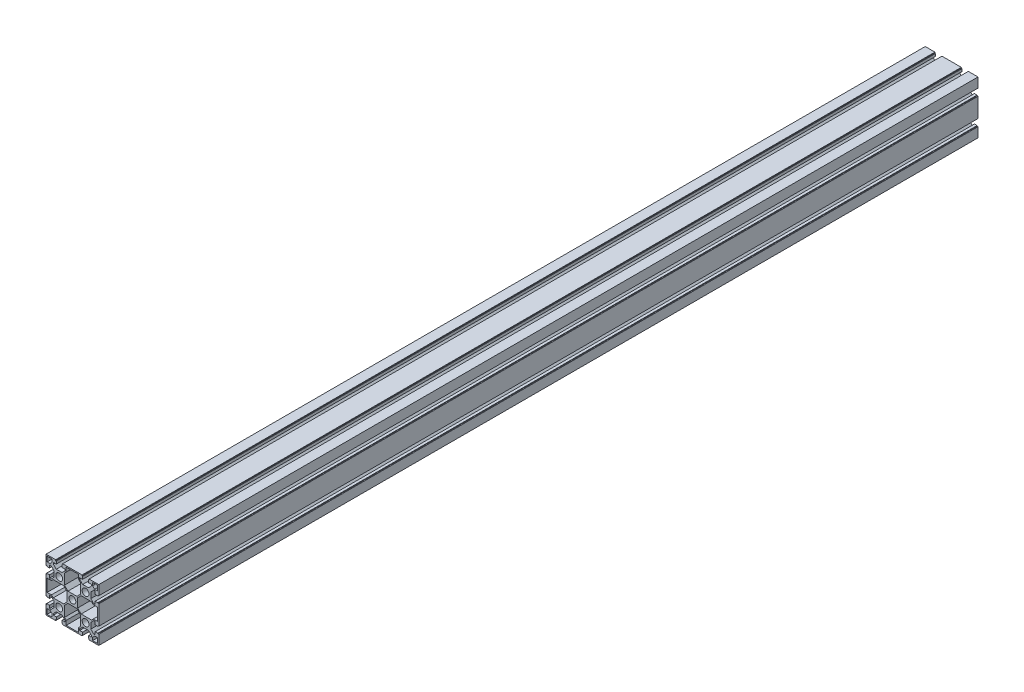
SolidWorks part; units mm, degrees
ref_plane "Alzado" through (0, 0, 0) normal (0, 0, 1) x (1, 0, 0)
ref_plane "Planta" through (0, 0, 0) normal (0, 1, 0) x (1, 0, 0)
ref_plane "Vista lateral" through (0, 0, 0) normal (1, 0, 0) x (0, 0, -1)
sketch "Croquis1" plane through (0, 0, 0) normal (0, 0, 1) x (1, 0, 0)
  line L0 (-1000, 0) -> (49000, 0) construction
  line L1 (0, -1000) -> (0, 49000) construction
  line L2 (-22.5, -999.7728) -> (-22.5, 49000.2272) construction
  line L7 (22.5, -999.7728) -> (22.5, 49000.2272) construction
  line L8 (-1000.2536, 22.5) -> (48999.7464, 22.5) construction
  line L9 (-1000.2536, -22.5) -> (48999.7464, -22.5) construction
  line L10 (-27.5, 31.5) -> (-32.5, 36.5)
  line L11 (-32.5, 36.5) -> (-32.5, 39)
  line L12 (-32.5, 39) -> (-27.5, 39)
  line L13 (-27.5, 39) -> (-27.5, 43.5)
  line L14 (-27.5, 43.5) -> (-28.5, 43.5)
  line L15 (-28.5, 43.5) -> (-28.5, 45)
  line L16 (-28.5, 45) -> (-45, 45)
  line L17 (-16.5, 45) -> (0, 45)
  line L18 (-16.5, 43.5) -> (-16.5, 45)
  line L19 (-17.5, 43.5) -> (-16.5, 43.5)
  line L20 (-17.5, 39) -> (-17.5, 43.5)
  line L21 (-12.5, 39) -> (-17.5, 39)
  line L22 (-12.5, 36.5) -> (-12.5, 39)
  line L23 (-17.5, 31.5) -> (-12.5, 36.5)
  line L24 (17.5, 31.5) -> (12.5, 36.5)
  line L25 (12.5, 36.5) -> (12.5, 39)
  line L26 (12.5, 39) -> (17.5, 39)
  line L27 (17.5, 43.5) -> (16.5, 43.5)
  line L28 (16.5, 43.5) -> (16.5, 45)
  line L29 (16.5, 45) -> (0, 45)
  line L30 (28.5, 45) -> (45, 45)
  line L31 (28.5, 43.5) -> (28.5, 45)
  line L32 (27.5, 43.5) -> (28.5, 43.5)
  line L33 (27.5, 39) -> (27.5, 43.5)
  line L34 (32.5, 39) -> (27.5, 39)
  line L35 (32.5, 36.5) -> (32.5, 39)
  line L36 (27.5, 31.5) -> (32.5, 36.5)
  line L37 (17.5, 43.5) -> (17.5, 39)
  line L38 (27.5, 31.5) -> (17.5, 31.5)
  line L39 (-17.5, 31.5) -> (-27.5, 31.5)
  line L40 (45, -28.5) -> (45, -45)
  line L41 (43.5, -28.5) -> (45, -28.5)
  line L42 (39, -27.5) -> (43.5, -27.5)
  line L43 (39, -32.5) -> (39, -27.5)
  line L44 (36.5, -32.5) -> (39, -32.5)
  line L45 (31.5, -27.5) -> (36.5, -32.5)
  line L46 (31.5, -27.5) -> (31.5, -17.5)
  line L47 (31.5, -17.5) -> (36.5, -12.5)
  line L48 (36.5, -12.5) -> (39, -12.5)
  line L49 (39, -12.5) -> (39, -17.5)
  line L50 (43.5, -17.5) -> (39, -17.5)
  line L51 (43.5, -17.5) -> (43.5, -16.5)
  line L52 (43.5, -16.5) -> (45, -16.5)
  line L53 (45, -16.5) -> (45, 0)
  line L54 (45, 16.5) -> (45, 0)
  line L55 (43.5, 16.5) -> (45, 16.5)
  line L56 (43.5, 17.5) -> (43.5, 16.5)
  line L57 (39, 17.5) -> (43.5, 17.5)
  line L58 (39, 12.5) -> (39, 17.5)
  line L59 (36.5, 12.5) -> (39, 12.5)
  line L60 (31.5, 17.5) -> (31.5, 27.5)
  line L61 (31.5, 17.5) -> (36.5, 12.5)
  line L62 (31.5, 27.5) -> (36.5, 32.5)
  line L63 (36.5, 32.5) -> (39, 32.5)
  line L64 (39, 32.5) -> (39, 27.5)
  line L65 (39, 27.5) -> (43.5, 27.5)
  line L66 (43.5, 27.5) -> (43.5, 28.5)
  line L67 (43.5, 28.5) -> (45, 28.5)
  line L68 (45, 28.5) -> (45, 45)
  line L69 (-28.5, -45) -> (-45, -45)
  line L70 (-28.5, -43.5) -> (-28.5, -45)
  line L71 (-27.5, -39) -> (-27.5, -43.5)
  line L72 (-32.5, -39) -> (-27.5, -39)
  line L73 (-32.5, -36.5) -> (-32.5, -39)
  line L74 (-27.5, -31.5) -> (-32.5, -36.5)
  line L75 (-27.5, -31.5) -> (-17.5, -31.5)
  line L76 (-17.5, -31.5) -> (-12.5, -36.5)
  line L77 (-12.5, -36.5) -> (-12.5, -39)
  line L78 (-12.5, -39) -> (-17.5, -39)
  line L79 (-17.5, -43.5) -> (-17.5, -39)
  line L80 (-17.5, -43.5) -> (-16.5, -43.5)
  line L81 (-16.5, -43.5) -> (-16.5, -45)
  line L82 (-16.5, -45) -> (0, -45)
  line L83 (16.5, -45) -> (0, -45)
  line L84 (16.5, -43.5) -> (16.5, -45)
  line L85 (17.5, -43.5) -> (16.5, -43.5)
  line L86 (17.5, -39) -> (17.5, -43.5)
  line L87 (12.5, -39) -> (17.5, -39)
  line L88 (12.5, -36.5) -> (12.5, -39)
  line L89 (17.5, -31.5) -> (27.5, -31.5)
  line L90 (17.5, -31.5) -> (12.5, -36.5)
  line L91 (27.5, -31.5) -> (32.5, -36.5)
  line L92 (32.5, -36.5) -> (32.5, -39)
  line L93 (32.5, -39) -> (27.5, -39)
  line L94 (27.5, -39) -> (27.5, -43.5)
  line L95 (27.5, -43.5) -> (28.5, -43.5)
  line L96 (28.5, -43.5) -> (28.5, -45)
  line L97 (28.5, -45) -> (45, -45)
  line L98 (-45, 28.5) -> (-45, 45)
  line L99 (-43.5, 28.5) -> (-45, 28.5)
  line L100 (-39, 27.5) -> (-43.5, 27.5)
  line L101 (-39, 32.5) -> (-39, 27.5)
  line L102 (-36.5, 32.5) -> (-39, 32.5)
  line L103 (-31.5, 27.5) -> (-36.5, 32.5)
  line L104 (-31.5, 27.5) -> (-31.5, 17.5)
  line L105 (-31.5, 17.5) -> (-36.5, 12.5)
  line L106 (-36.5, 12.5) -> (-39, 12.5)
  line L107 (-39, 12.5) -> (-39, 17.5)
  line L108 (-43.5, 17.5) -> (-39, 17.5)
  line L109 (-43.5, 17.5) -> (-43.5, 16.5)
  line L110 (-43.5, 16.5) -> (-45, 16.5)
  line L111 (-45, 16.5) -> (-45, 0)
  line L112 (-45, -16.5) -> (-45, 0)
  line L113 (-43.5, -16.5) -> (-45, -16.5)
  line L114 (-43.5, -17.5) -> (-43.5, -16.5)
  line L115 (-39, -17.5) -> (-43.5, -17.5)
  line L116 (-39, -12.5) -> (-39, -17.5)
  line L117 (-36.5, -12.5) -> (-39, -12.5)
  line L118 (-31.5, -17.5) -> (-31.5, -27.5)
  line L119 (-31.5, -17.5) -> (-36.5, -12.5)
  line L120 (-31.5, -27.5) -> (-36.5, -32.5)
  line L121 (-36.5, -32.5) -> (-39, -32.5)
  line L122 (-39, -32.5) -> (-39, -27.5)
  line L123 (-39, -27.5) -> (-43.5, -27.5)
  line L124 (-43.5, -27.5) -> (-43.5, -28.5)
  line L125 (-43.5, -28.5) -> (-45, -28.5)
  line L126 (-45, -28.5) -> (-45, -45)
  line L127 (-0.0008, 43) -> (-10.5, 43)
  line L129 (-13.5, 14.9142) -> (-7.5858, 9)
  line L130 (-7.5858, 9) -> (-0.2469, 9)
  line L131 (7.5858, 9) -> (-0.2469, 9)
  line L132 (13.5, 14.9142) -> (7.5858, 9)
  line L134 (-0.0008, 43) -> (10.5, 43)
  line L135 (-43.5, 28.5) -> (-43.5, 27.5)
  line L136 (-27.5, -43.5) -> (-28.5, -43.5)
  line L137 (43.5, -27.5) -> (43.5, -28.5)
  line L162 (-45, 45) -> (0, 0) construction
  line L163 (-43, 43) -> (-43, 34.5)
  line L164 (-43, 43) -> (-34.5, 43)
  line L165 (-43, 34.5) -> (-38, 34.5)
  line L166 (-34.5, 43) -> (-34.5, 38)
  line L167 (-34.5, 38) -> (-38, 34.5)
  line L168 (38, 34.5) -> (34.5, 38)
  line L169 (34.5, 43) -> (34.5, 38)
  line L170 (43, 43) -> (34.5, 43)
  line L171 (43, 43) -> (43, 34.5)
  line L172 (43, 34.5) -> (38, 34.5)
  line L173 (34.5, -38) -> (38, -34.5)
  line L174 (43, -34.5) -> (38, -34.5)
  line L175 (43, -43) -> (43, -34.5)
  line L176 (43, -43) -> (34.5, -43)
  line L177 (34.5, -43) -> (34.5, -38)
  line L178 (-38, -34.5) -> (-34.5, -38)
  line L179 (-34.5, -43) -> (-34.5, -38)
  line L180 (-43, -43) -> (-34.5, -43)
  line L181 (-43, -43) -> (-43, -34.5)
  line L182 (-43, -34.5) -> (-38, -34.5)
  line L183 (-10.5, 43) -> (-10.5, 35.6716)
  line L184 (-10.5, 35.6716) -> (-13.5, 32.6716)
  line L185 (-13.5, 32.6716) -> (-13.5, 14.9142)
  line L186 (13.5, 32.6716) -> (13.5, 14.9142)
  line L187 (10.5, 35.6716) -> (13.5, 32.6716)
  line L188 (10.5, 43) -> (10.5, 35.6716)
  line L189 (32.6716, -13.5) -> (14.9142, -13.5)
  line L190 (14.9142, -13.5) -> (9, -7.5858)
  line L191 (9, -7.5858) -> (9, 0.2469)
  line L192 (9, 7.5858) -> (9, 0.2469)
  line L193 (14.9142, 13.5) -> (9, 7.5858)
  line L194 (32.6716, 13.5) -> (14.9142, 13.5)
  line L195 (35.6716, 10.5) -> (32.6716, 13.5)
  line L196 (43, 10.5) -> (35.6716, 10.5)
  line L197 (43, 0.0008) -> (43, 10.5)
  line L198 (43, 0.0008) -> (43, -10.5)
  line L199 (43, -10.5) -> (35.6716, -10.5)
  line L200 (35.6716, -10.5) -> (32.6716, -13.5)
  line L201 (-13.5, -32.6716) -> (-13.5, -14.9142)
  line L202 (-13.5, -14.9142) -> (-7.5858, -9)
  line L203 (-7.5858, -9) -> (0.2469, -9)
  line L204 (7.5858, -9) -> (0.2469, -9)
  line L205 (13.5, -14.9142) -> (7.5858, -9)
  line L206 (13.5, -32.6716) -> (13.5, -14.9142)
  line L207 (10.5, -35.6716) -> (13.5, -32.6716)
  line L208 (10.5, -43) -> (10.5, -35.6716)
  line L209 (0.0008, -43) -> (10.5, -43)
  line L210 (0.0008, -43) -> (-10.5, -43)
  line L211 (-10.5, -43) -> (-10.5, -35.6716)
  line L212 (-10.5, -35.6716) -> (-13.5, -32.6716)
  line L213 (-32.6716, 13.5) -> (-14.9142, 13.5)
  line L214 (-14.9142, 13.5) -> (-9, 7.5858)
  line L215 (-9, 7.5858) -> (-9, -0.2469)
  line L216 (-9, -7.5858) -> (-9, -0.2469)
  line L217 (-14.9142, -13.5) -> (-9, -7.5858)
  line L218 (-32.6716, -13.5) -> (-14.9142, -13.5)
  line L219 (-35.6716, -10.5) -> (-32.6716, -13.5)
  line L220 (-43, -10.5) -> (-35.6716, -10.5)
  line L221 (-43, -0.0008) -> (-43, -10.5)
  line L222 (-43, -0.0008) -> (-43, 10.5)
  line L223 (-43, 10.5) -> (-35.6716, 10.5)
  line L224 (-35.6716, 10.5) -> (-32.6716, 13.5)
  circle A0 centre (0, 0) radius 5.85
  circle A5 centre (-22.5, 22.5) radius 5.85
  circle A6 centre (22.5, 22.5) radius 5.85
  circle A7 centre (-22.5, -22.5) radius 5.85
  circle A8 centre (22.5, -22.5) radius 5.85
  point P146 (0, 0)
  point P179 (0, 0)
  point P200 (0, 0)
  point P217 (0, 0)
  dimension "D1" = 11.7
  dimension "D4" = 11.7
  dimension "D5" = 11.7
  dimension "D17" = 9
  dimension "D2" = 45
  dimension "D3" = 45
  dimension "D6" = 90
  dimension "D7" = 12.5
  dimension "D8" = 12
  dimension "D9" = 10
  dimension "D10" = 6
  dimension "D11" = 1.5
  dimension "D12" = 9
  dimension "D13" = 4
  dimension "D14" = 9
  dimension "D15" = 2
  dimension "D16" = 2
  dimension "D19" = 2
  dimension "D20" = 4
  dimension "D21" = 2
  dimension "D22" = 2
  dimension "D23" = 5
  dimension "D24" = 5
  dimension "D25" = 2
  dimension "D18" = 9
  dimension "D27" = 2
  dimension "D28" = 2
  dimension "D26" = 4
extrude "Saliente-Extruir2" add sketch "Croquis1" along normal mid plane 1500
sketch "Croquis2" [suppressed] plane through (0, 0, 0) normal (0, 1, 0) x (1, 0, 0)
  line L0 (-45, 0) -> (45, 0)
  line L1 (45, 0) -> (45, -51.9615)
  line L2 (45, -209.019) -> (45, 0) construction
  line L3 (45, -51.9615) -> (-45, 0)
  line L4 (-45, -209.019) -> (-45, 0) construction
  dimension "D1" = 60
extrude "Cortar-Extruir1" [suppressed] cut sketch "Croquis2" against normal through all both and the other way through all
hole_wizard "Taladro de margen para M101" [suppressed] positions "Croquis3" profile "Croquis4" hole size "M10" standard "ISO"
sketch "Croquis3" plane through (45, 0, 0) normal (1, 0, 0) x (0, 0, -1)
  line L0 (0, -1000) -> (0, 49000) construction
  point P0 (-35, 22.5)
  point P9 (35, 22.5)
  dimension "D1" = 70
  dimension "D2" = 22.5
sketch "Croquis4" plane through (45, 22.5, 35) normal (0, 1, 0) x (0, 0, -1)
  line L0 (0, 0) -> (0, 90)
  line L1 (0, 90) -> (5.25, 90)
  line L2 (5.25, 90) -> (5.25, 0)
  line L5 (5.25, 0) -> (0, 0)
  line L11 (0, -6.35) -> (0, 107.95) construction
  dimension "Diámetro de taladro hasta el siguiente" = 10.5
  dimension "Profundidad de taladro hasta el siguiente" = 90
hole_wizard "Taladro de margen para M61" positions "Croquis5" profile "Croquis6" hole size "M6" standard "ISO" end condition through all
sketch "Croquis5" plane through (0, 45, 0) normal (0, 1, 0) x (1, 0, 0)
  line L0 (0, -1000) -> (0, 49000) construction
  line L1 (-1000, 0) -> (49000, 0) construction
  point P0 (-22.5, 26)
  point P14 (-22.5, -26)
  point P15 (22.5, -26)
  point P16 (22.5, 26)
  dimension "D1" = 45
  dimension "D2" = 52
sketch "Croquis6" plane through (-22.5, 45, -26) normal (1, 0, 0) x (0, 0, 1)
  line L0 (0, 0) -> (0, 90)
  line L1 (0, 90) -> (3.2, 90)
  line L2 (3.2, 90) -> (3.2, 0)
  line L5 (3.2, 0) -> (0, 0)
  line L11 (0, -6.35) -> (0, 107.95) construction
  dimension "Diámetro de taladro hasta el siguiente" = 6.4
  dimension "Profundidad de taladro hasta el siguiente" = 90
sketch "Croquis7" [suppressed] plane through (0, 0, 0) normal (0, 1, 0) x (1, 0, 0)
  line L0 (-45, 230.94) -> (45, 230.94)
  line L1 (45, 230.94) -> (45, 178.9785)
  line L2 (45, -230.94) -> (45, 230.94) construction
  line L3 (45, 178.9785) -> (-45, 230.94)
  line L4 (-45, -230.94) -> (-45, -178.9785)
  line L5 (-45, -230.94) -> (-45, 230.94) construction
  line L6 (-45, -178.9785) -> (45, -230.94)
  line L7 (45, -230.94) -> (-45, -230.94)
  dimension "D1" = 30
  dimension "D2" = 30
extrude "Cortar-Extruir2" [suppressed] cut sketch "Croquis7" against normal through all both and the other way through all
